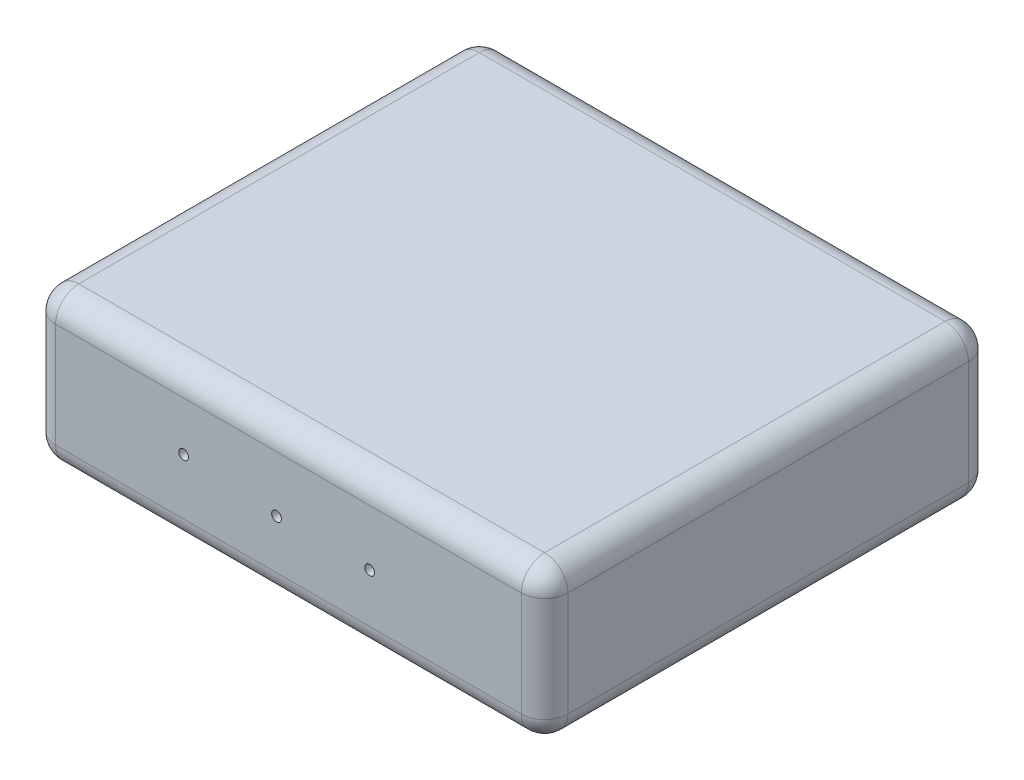
SolidWorks part; units mm, degrees
ref_plane "Front Plane" through (0, 0, 0) normal (0, 0, 1) x (1, 0, 0)
ref_plane "Top Plane" through (0, 0, 0) normal (0, 1, 0) x (1, 0, 0)
ref_plane "Right Plane" through (0, 0, 0) normal (1, 0, 0) x (0, 0, -1)
sketch "Sketch1" plane through (0, 0, 0) normal (0, 1, 0) x (1, 0, 0)
  line L1 (110, -96) -> (-110, -96)
  line L2 (110, -96) -> (110, 96)
  line L3 (110, 96) -> (-110, 96)
  line L4 (-110, -96) -> (-110, 96)
  line L5 (110, -96) -> (-110, 96) construction
  line L6 (110, 96) -> (-110, -96) construction
  point P0 (0, 0)
  dimension "D1" = 220
  dimension "D2" = 192
extrude "Boss-Extrude1" add sketch "Sketch1" along normal blind 65
fillet "Fillet1" radius 10 12 edges at (110, 32.5, 96) (110, 0, 0) (110, 32.5, -96) (0, 0, -96) (-110, 0, 0) (0, 0, 96) (-110, 32.5, -96) (-110, 32.5, 96) (110, 65, 0) (0, 65, -96) (-110, 65, 0) (0, 65, 96)
hole_wizard "Ø4.2 (4.2) Diameter Hole1" positions "Sketch3" profile "Sketch2" hole size "Ø4.2" standard "ANSI Metric"
sketch "Sketch3" plane through (0, 0, 96) normal (0, 0, 1) x (1, 0, 0)
  line L0 (-110, 10) -> (-110, 55) construction
  line L1 (-100, 65) -> (100, 65) construction
  point P0 (-45, 34)
  point P2 (-5.112, 31.0084)
  point P4 (34.888, 31)
  dimension "D1" = 40
  dimension "D2" = 40
  dimension "D3" = 65
  dimension "D4" = 31
sketch "Sketch2" plane through (-45, 34, 96) normal (1, 0, 0) x (0, -1, 0)
  line L0 (0, 0) -> (0, 11.2618)
  line L1 (0, 11.2618) -> (2.1, 10)
  line L2 (2.1, 10) -> (2.1, 0)
  line L5 (2.1, 0) -> (0, 0)
  line L10 (0, 11.2618) -> (-2.1, 10) construction
  line L11 (0, -6.35) -> (0, 107.95) construction
  dimension "Hole Dia." = 4.2
  dimension "Hole Depth" = 10
  dimension "Drill Angle" = 118
hole_wizard "Ø4.2 (4.2) Diameter Hole2" positions "Sketch4" profile "Sketch5" hole size "Ø4.2" standard "ANSI Metric"
sketch "Sketch4" plane through (0, 0, -96) normal (0, 0, -1) x (-1, 0, 0)
  line L2 (-110, 10) -> (-110, 55) construction
  line L3 (-100, 65) -> (100, 65) construction
  point P0 (-45, 34)
  point P2 (-5.112, 31.0084)
  point P4 (34.888, 31)
  dimension "D1" = 40
  dimension "D2" = 40
  dimension "D3" = 65
  dimension "D4" = 31
sketch "Sketch5" plane through (45, 34, -96) normal (1, 0, 0) x (0, 1, 0)
  line L0 (0, 0) -> (0, 11.2618)
  line L1 (0, 11.2618) -> (2.1, 10)
  line L2 (2.1, 10) -> (2.1, 0)
  line L5 (2.1, 0) -> (0, 0)
  line L10 (0, 11.2618) -> (-2.1, 10) construction
  line L11 (0, -6.35) -> (0, 107.95) construction
  dimension "Hole Dia." = 4.2
  dimension "Hole Depth" = 10
  dimension "Drill Angle" = 118
equation "\"connector_D1\" = 70 'the big holes diameter"
equation "\"mtg_hole_D\" = 5.5 'mounting holes"
equation "\"mtg_dfc\" = 40 'mounting hole distance from center"
equation "\"plate_thickness\" = 6.35 'thickness of the plate "
equation "\"t_height\" = 200"
equation "\"t_width\" = 240"
equation "\"t_length\" = 240"
equation "\"plate_hole_from_edge\" = 9"
equation "\"plate_spacing\" = 1"
equation "\"front_plate_height\" = \"t_height\" + 38"
equation "\"front_plate_width\" = \"t_width\" + 38"
equation "\"side_plate_height\" = \"front_plate_height\""
equation "\"side_plate_length\" = \"t_length\" + 38"
equation "\"top_plate_width\" = \"front_plate_width\""
equation "\"top_plate_length\" = \"side_plate_length\""
equation "\"itx_support_t_slot_length\" = \"t_width\" + (2 * 20.5)"
equation "\"locomotion_length\" = \"t_length\""
equation "\"locomotion_width\" = \"t_width\""
equation "\"locomotion_height\" = 40"
equation "\"itx_mtg_hole_spacing\" = 40"
equation "\"D1@Sketch3\"=\"itx_mtg_hole_spacing\""
equation "\"D2@Sketch3\"=\"itx_mtg_hole_spacing\""
equation "\"D3@Sketch3\"=105 - 40"
